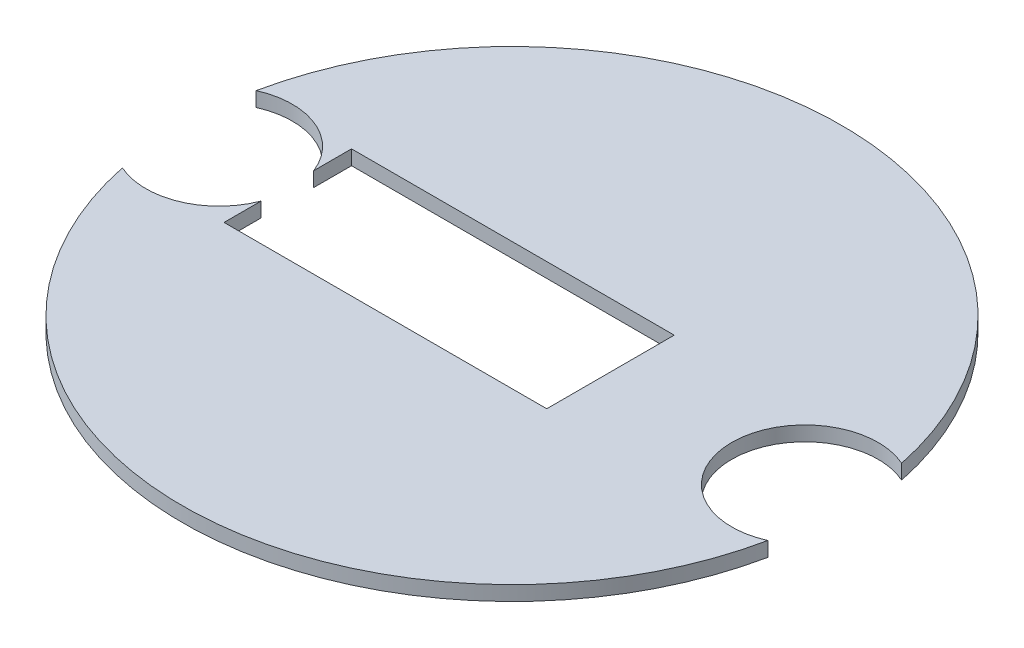
SolidWorks part; units mm, degrees
ref_plane "Front Plane" through (0, 0, 0) normal (0, 0, 1) x (1, 0, 0)
ref_plane "Top Plane" through (0, 0, 0) normal (0, 1, 0) x (1, 0, 0)
ref_plane "Right Plane" through (0, 0, 0) normal (1, 0, 0) x (0, 0, -1)
sketch "Sketch1" plane through (0, 0, 0) normal (0, 1, 0) x (1, 0, 0)
  circle A0 centre (0, 0) radius 57.15
extrude "Boss-Extrude1" add sketch "Sketch1" along normal blind 2.54
sketch "Sketch3" plane through (0, 2.54, 0) normal (0, 1, 0) x (1, 0, 0)
  line L0 (41.4882, -39.3046) -> (41.4882, 39.3046)
  line L1 (-41.4882, -39.3046) -> (-41.4882, 39.3046)
  line L3 (-38.95, -10.9848) -> (17.0089, -10.9848)
  line L4 (-38.95, -10.9848) -> (-38.95, 11.1221)
  line L5 (-38.95, 11.1221) -> (17.0089, 11.1221)
  line L6 (17.0089, -10.9848) -> (17.0089, 11.1221)
  circle A2 centre (0, 0) radius 57.15 construction
extrude "Cut-Extrude1" cut sketch "Sketch3" against normal blind 2.54 contours L5 L6 L3 L4
sketch "Sketch4" plane through (0, 0, 0) normal (0, -1, 0) x (-1, 0, 0)
  circle A0 centre (50.8, 0) radius 12.7
extrude "Cut-Extrude2" cut sketch "Sketch4" against normal blind 2.54
sketch "Sketch5" plane through (0, 0, 0) normal (0, -1, 0) x (1, 0, 0)
  circle A0 centre (50.8, 0) radius 12.7
extrude "Cut-Extrude3" cut sketch "Sketch5" against normal blind 2.54
